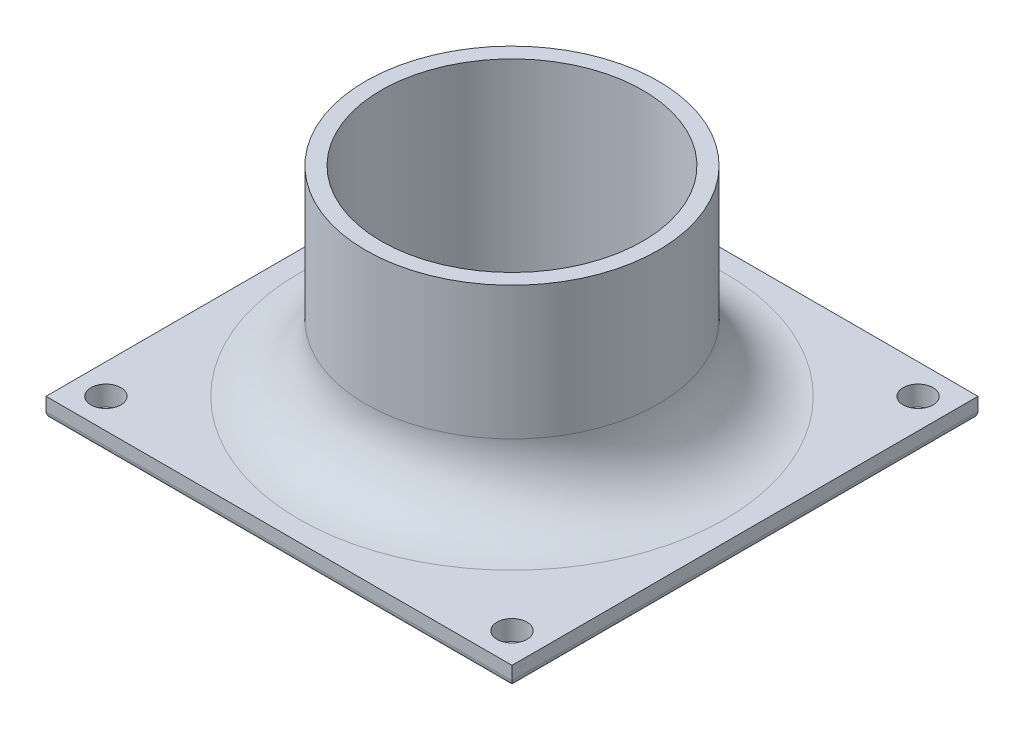
SolidWorks part; units mm, degrees
ref_plane "Front Plane" through (0, 0, 0) normal (0, 0, 1) x (1, 0, 0)
ref_plane "Top Plane" through (0, 0, 0) normal (0, 1, 0) x (1, 0, 0)
ref_plane "Right Plane" through (0, 0, 0) normal (1, 0, 0) x (0, 0, -1)
sketch "Sketch1" plane through (0, 0, 0) normal (0, 1, 0) x (1, 0, 0)
  line L1 (-35, 35) -> (35, 35)
  line L2 (-35, 35) -> (-35, -35)
  line L3 (-35, -35) -> (35, -35)
  line L4 (35, 35) -> (35, -35)
  line L5 (-35, 35) -> (35, -35) construction
  line L6 (-35, -35) -> (35, 35) construction
  point P0 (0, 0)
  dimension "D1" = 70
  dimension "D2" = 70
extrude "Boss-Extrude1" add sketch "Sketch1" along normal blind 3
sketch "Sketch2" plane through (0, 3, 0) normal (0, 1, 0) x (1, 0, 0)
  circle A0 centre (0, 0) radius 18
  dimension "D1" = 36
extrude "Cut-Extrude1" cut sketch "Sketch2" against normal blind 3
sketch "Sketch3" plane through (0, 3, 0) normal (0, 1, 0) x (1, 0, 0)
  circle A0 centre (0, 0) radius 19.65
  circle A1 centre (0, 0) radius 22
  dimension "D1" = 39.3
  dimension "D2" = 44
extrude "Boss-Extrude2" add sketch "Sketch3" along normal blind 30
fillet "Fillet1" radius 10 1 edges at (0, 3, 22)
sketch "Sketch4" plane through (0, 0, 0) normal (0, -1, 0) x (-1, 0, 0)
  line L0 (35, -35) -> (-35, -35) construction
  line L2 (35, 35) -> (35, -35) construction
  circle A0 centre (30.5, -30.5) radius 2.25
  dimension "D1" = 4.5
  dimension "D2" = 4.5
  dimension "D3" = 4.5
extrude "Cut-Extrude2" cut sketch "Sketch4" against normal blind 3
sketch "Sketch5" plane through (0, 0, 0) normal (0, -1, 0) x (-1, 0, 0)
  line L0 (0, -35) -> (0, 35) construction
  line L1 (35, -35) -> (-35, -35) construction
  line L2 (-35, 35) -> (35, 35) construction
  line L3 (35, 0) -> (-35, 0) construction
  line L4 (35, 35) -> (35, -35) construction
  line L5 (-35, -35) -> (-35, 35) construction
mirror "Mirror1" about plane through (0, 0, 0) normal (1, 0, 0) of "Cut-Extrude2" second plane through (0, 0, 0) second plane normal (0, 0, 1)
fillet "Fillet4" radius 1 4 edges at (0, 0, 35) (-35, 0, 0) (0, 0, -35) (35, 0, 0)
